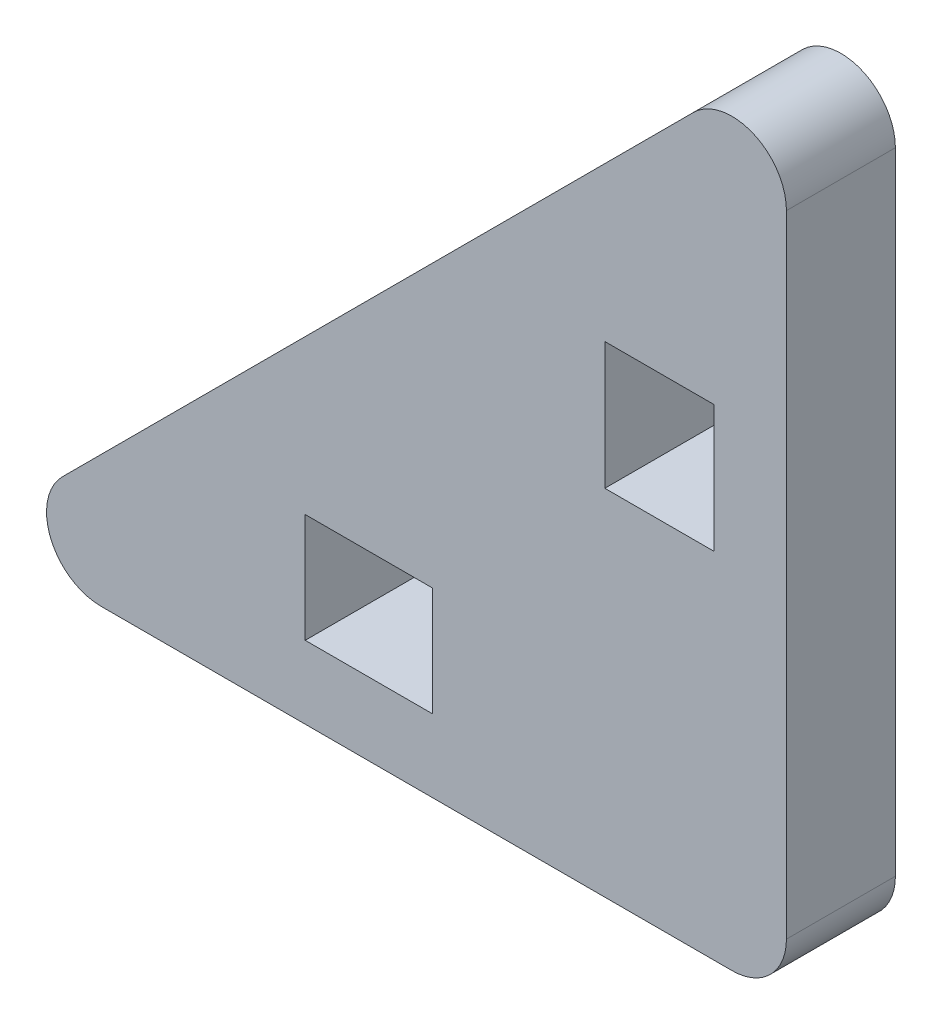
SolidWorks part; units mm, degrees
ref_plane "Спереди" through (0, 0, 0) normal (0, 0, 1) x (1, 0, 0)
ref_plane "Сверху" through (0, 0, 0) normal (0, 1, 0) x (1, 0, 0)
ref_plane "Справа" through (0, 0, 0) normal (1, 0, 0) x (0, 0, -1)
sketch "Эскиз1" plane through (0, 0, 0) normal (0, 0, 1) x (1, 0, 0)
  line L0 (0, 0) -> (-22.4926, 0)
  line L1 (-22.4926, 0) -> (0, 22.4926)
  line L2 (0, 22.4926) -> (0, 0)
  line L3 (-13.25, 2) -> (-9.75, 2)
  line L8 (-5, 9.75) -> (-2, 9.75)
  line L9 (-5, 9.75) -> (-5, 13.25)
  line L10 (-5, 13.25) -> (-2, 13.25)
  line L11 (-2, 9.75) -> (-2, 13.25)
  line L12 (-5, 9.75) -> (-2, 13.25) construction
  line L13 (-5, 13.25) -> (-2, 9.75) construction
  line L14 (-13.25, 2) -> (-13.25, 5)
  line L15 (-13.25, 5) -> (-9.75, 5)
  line L16 (-9.75, 2) -> (-9.75, 5)
  line L17 (-13.25, 2) -> (-9.75, 5) construction
  line L18 (-13.25, 5) -> (-9.75, 2) construction
  point P2 (-3.5, 11.5)
  point P8 (-11.5, 3.5)
  dimension "D1" = 3
  dimension "D2" = 3.5
  dimension "D3" = 3.5
  dimension "D4" = 3.5
  dimension "D5" = 7.75
  dimension "D6" = 7.75
  dimension "D7" = 3
extrude "Бобышка-Вытянуть1" add sketch "Эскиз1" along normal blind 3 contours L2 L1 L0 L16 L3 L14 L15 L11 L8 L9 L10
fillet "Скругление1" radius 1.5 3 edges at (0, 0, 1.5) (-22.4926, 0, 1.5) (0, 22.4926, 1.5)
